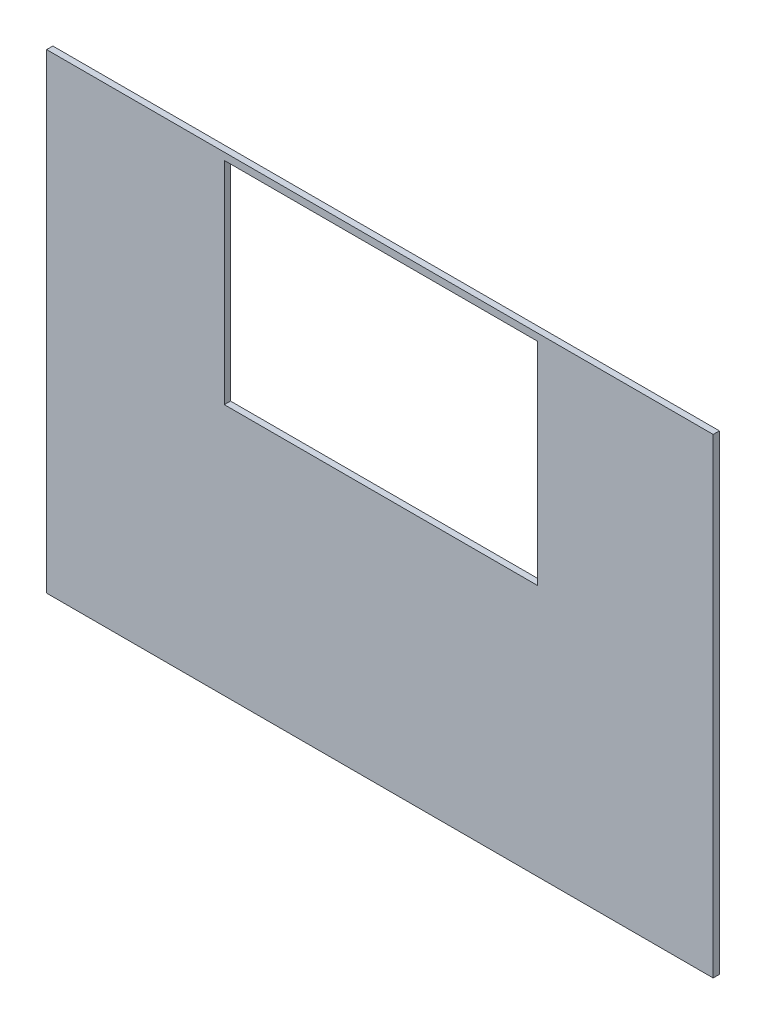
SolidWorks part; units mm, degrees
ref_plane "Front Plane" through (0, 0, 0) normal (0, 0, 1) x (1, 0, 0)
ref_plane "Top Plane" through (0, 0, 0) normal (0, 1, 0) x (1, 0, 0)
ref_plane "Right Plane" through (0, 0, 0) normal (1, 0, 0) x (0, 0, -1)
sketch "Sketch1" plane through (0, 0, 0) normal (0, 0, 1) x (1, 0, 0)
  line L1 (0, 0) -> (681.08, 0)
  line L2 (0, 0) -> (0, -481.0026)
  line L3 (0, -481.0026) -> (681.08, -481.0026)
  line L4 (681.08, 0) -> (681.08, -481.0026)
  dimension "D1" = 681.08
  dimension "D2" = 481.0026
extrude "Boss-Extrude1" add sketch "Sketch1" along normal blind 6.35
sketch "Sketch2" plane through (0, 0, 0) normal (0, 0, -1) x (-1, 0, 0)
  line L0 (-181.5418, -461.0026) -> (-181.5418, -59.0026) construction
  line L1 (-501.3881, -223.4089) -> (-181.5418, -223.4089)
  line L2 (-501.3881, -223.4089) -> (-501.3881, -7.2954)
  line L3 (-501.3881, -7.2954) -> (-181.5418, -7.2954)
  line L4 (-181.5418, -223.4089) -> (-181.5418, -7.2954)
  line L6 (-181.5418, -223.4089) -> (-501.7218, -223.4089) construction
  line L7 (-501.3881, -461.0026) -> (-501.3881, -59.0026) construction
extrude "Cut-Extrude1" cut sketch "Sketch2" against normal blind 10
